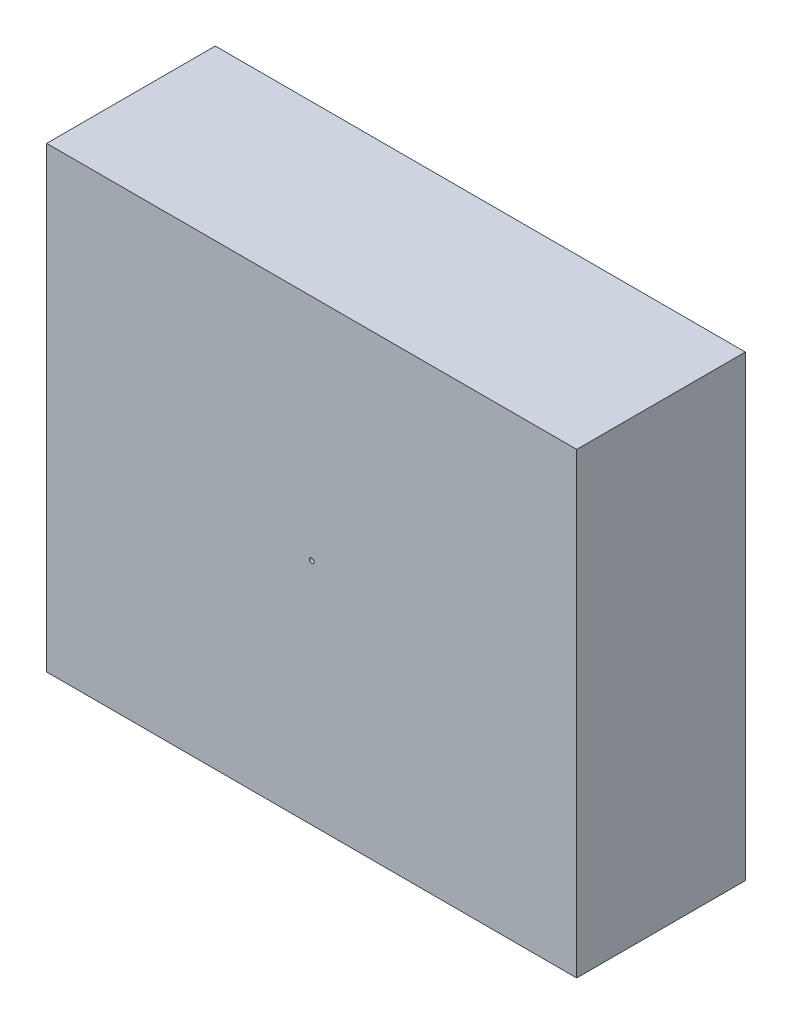
SolidWorks part; units mm, degrees
ref_plane "Plan de face" through (0, 0, 0) normal (0, 0, 1) x (1, 0, 0)
ref_plane "Plan de dessus" through (0, 0, 0) normal (0, 1, 0) x (1, 0, 0)
ref_plane "Plan de droite" through (0, 0, 0) normal (1, 0, 0) x (0, 0, -1)
sketch "Esquisse1" plane through (0, 0, 0) normal (0, 0, 1) x (1, 0, 0)
  line L1 (0, 0) -> (-220, 0)
  line L2 (0, 0) -> (0, 190)
  line L3 (0, 190) -> (-220, 190)
  line L4 (-220, 0) -> (-220, 190)
  dimension "D1" = 220
  dimension "D2" = 190
extrude "Boss.-Extru.1" add sketch "Esquisse1" along normal blind 70
sketch "Esquisse2" plane through (0, 0, 0) normal (0, 0, -1) x (-1, 0, 0)
  line L0 (110, 0) -> (110, 190) construction
  line L1 (220, 0) -> (0, 0) construction
  line L2 (0, 190) -> (220, 190) construction
  line L3 (220, 95) -> (0, 95) construction
  line L4 (220, 190) -> (220, 0) construction
  line L5 (0, 0) -> (0, 190) construction
  circle A0 centre (110, 95) radius 1
  point P14 (0, 0)
  point P15 (110, 95)
  dimension "D1" = 2
extrude "Enlèv. mat.-Extru.1" cut sketch "Esquisse2" along normal blind 10 and the other way blind 119
